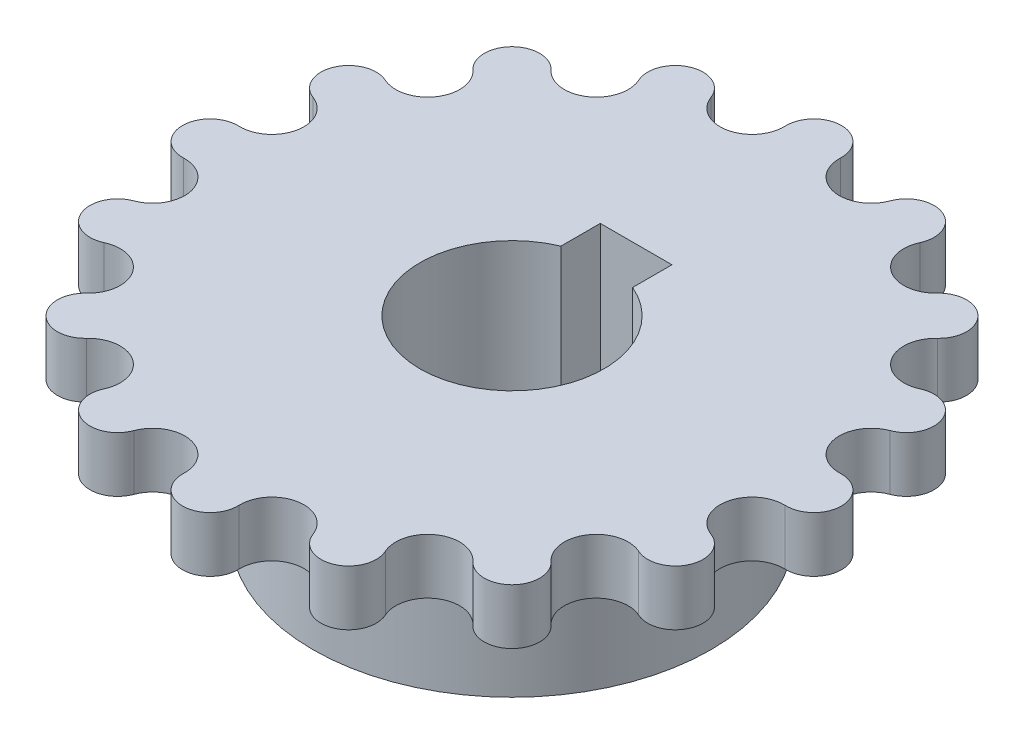
SolidWorks part; units mm, degrees
ref_plane "Front Plane" through (0, 0, 0) normal (0, 0, 1) x (1, 0, 0)
ref_plane "Top Plane" through (0, 0, 0) normal (0, 1, 0) x (1, 0, 0)
ref_plane "Right Plane" through (0, 0, 0) normal (1, 0, 0) x (0, 0, -1)
sketch "Sketch2" plane through (0, 0, 0) normal (0, 1, 0) x (1, 0, 0)
  circle A0 centre (0, 0) radius 10.795
  dimension "D1" = 21.59
extrude "Boss-Extrude1" add sketch "Sketch2" along normal blind 10.287
sketch "Sketch3" plane through (0, 10.287, 0) normal (0, 1, 0) x (1, 0, 0)
  circle A0 centre (0, 0) radius 17.8689
  dimension "D1" = 35.7378
extrude "Boss-Extrude2" add sketch "Sketch3" against normal blind 2.9972
sketch "Sketch4" plane through (0, 10.287, 0) normal (0, 1, 0) x (1, 0, 0)
  arc A0 (1.4986, 16.3143) -> (-1.4986, 16.3143) centre (0, 16.3693) ccw
  circle A2 centre (0, 0) radius 17.8689 construction
  arc A3 (1.4986, 16.3143) -> (4.8587, 15.646) centre (3.2325, 16.2507) ccw
  arc A4 (7.6277, 14.499) -> (10.4763, 12.5956) centre (9.2053, 13.7767) ccw
  arc A5 (7.6277, 14.499) -> (4.8587, 15.646) centre (6.2643, 15.1233) ccw
  arc A6 (12.5956, 10.4763) -> (14.499, 7.6277) centre (13.7767, 9.2053) ccw
  arc A7 (12.5956, 10.4763) -> (10.4763, 12.5956) centre (11.5748, 11.5748) ccw
  arc A8 (15.646, 4.8587) -> (16.3143, 1.4986) centre (16.2507, 3.2325) ccw
  arc A9 (15.646, 4.8587) -> (14.499, 7.6277) centre (15.1233, 6.2643) ccw
  arc A10 (16.3143, -1.4986) -> (15.646, -4.8587) centre (16.2507, -3.2325) ccw
  arc A11 (16.3143, -1.4986) -> (16.3143, 1.4986) centre (16.3693, 0) ccw
  arc A12 (14.499, -7.6277) -> (12.5956, -10.4763) centre (13.7767, -9.2053) ccw
  arc A13 (14.499, -7.6277) -> (15.646, -4.8587) centre (15.1233, -6.2643) ccw
  arc A14 (10.4763, -12.5956) -> (7.6277, -14.499) centre (9.2053, -13.7767) ccw
  arc A15 (10.4763, -12.5956) -> (12.5956, -10.4763) centre (11.5748, -11.5748) ccw
  arc A16 (4.8587, -15.646) -> (1.4986, -16.3143) centre (3.2325, -16.2507) ccw
  arc A17 (4.8587, -15.646) -> (7.6277, -14.499) centre (6.2643, -15.1233) ccw
  arc A18 (-1.4986, -16.3143) -> (-4.8587, -15.646) centre (-3.2325, -16.2507) ccw
  arc A19 (-1.4986, -16.3143) -> (1.4986, -16.3143) centre (0, -16.3693) ccw
  arc A20 (-7.6277, -14.499) -> (-10.4763, -12.5956) centre (-9.2053, -13.7767) ccw
  arc A21 (-7.6277, -14.499) -> (-4.8587, -15.646) centre (-6.2643, -15.1233) ccw
  arc A22 (-12.5956, -10.4763) -> (-14.499, -7.6277) centre (-13.7767, -9.2053) ccw
  arc A23 (-12.5956, -10.4763) -> (-10.4763, -12.5956) centre (-11.5748, -11.5748) ccw
  arc A24 (-15.646, -4.8587) -> (-16.3143, -1.4986) centre (-16.2507, -3.2325) ccw
  arc A25 (-15.646, -4.8587) -> (-14.499, -7.6277) centre (-15.1233, -6.2643) ccw
  arc A26 (-16.3143, 1.4986) -> (-15.646, 4.8587) centre (-16.2507, 3.2325) ccw
  arc A27 (-16.3143, 1.4986) -> (-16.3143, -1.4986) centre (-16.3693, 0) ccw
  arc A28 (-14.499, 7.6277) -> (-12.5956, 10.4763) centre (-13.7767, 9.2053) ccw
  arc A29 (-14.499, 7.6277) -> (-15.646, 4.8587) centre (-15.1233, 6.2643) ccw
  arc A30 (-10.4763, 12.5956) -> (-7.6277, 14.499) centre (-9.2053, 13.7767) ccw
  arc A31 (-10.4763, 12.5956) -> (-12.5956, 10.4763) centre (-11.5748, 11.5748) ccw
  arc A32 (-4.8587, 15.646) -> (-1.4986, 16.3143) centre (-3.2325, 16.2507) ccw
  arc A33 (-4.8587, 15.646) -> (-7.6277, 14.499) centre (-6.2643, 15.1233) ccw
  circle A34 centre (0, 0) radius 16.383
  point P84 (0, 0)
  circle M33 centre (0, 0) radius 17.8689
  dimension "D2" = 32.766
  dimension "D3" = 2.9972
  dimension "D1" = 16
extrude "Cut-Extrude1" cut sketch "Sketch4" against normal through all contours A34 A5 A0 M33 | A3 A34 | A34 A7 A5 M33 | A4 A34 | A34 A9 A7 M33 | A6 A34 | A34 A11 A9 M33 | A8 A34 | A34 A13 A11 M33 | A10 A34 | A34 A15 A13 M33 | A12 A34 | A34 A17 A15 M33 | A14 A34 | A34 A19 A17 M33 | A16 A34 | A34 A21 A19 M33 | A18 A34 | A20 A34 | A34 A25 A23 M33 | A22 A34 | A34 A27 A25 M33 | A24 A34 | A34 A29 A27 M33 | A26 A34 | A34 A31 A29 M33 | A28 A34 | A34 A33 A31 M33 | A30 A34 | A32 A34 | A34 A0 A33 M33 | A34 A23 A21 M33
sketch "Sketch5" plane through (0, 10.287, 0) normal (0, 1, 0) x (1, 0, 0)
  line L2 (-1.9431, 4.5973) -> (-1.9431, 6.731)
  line L3 (-1.9431, 6.731) -> (1.9431, 6.731)
  line L4 (1.9431, 4.5973) -> (1.9431, 6.731)
  arc A0 (-1.9431, 4.5973) -> (1.9431, 4.5973) centre (0, 0) ccw
  point P7 (0, 6.731)
  dimension "D1" = 9.9822
  dimension "D2" = 6.731
  dimension "D3" = 3.8862
extrude "Cut-Extrude2" cut sketch "Sketch5" against normal through all
